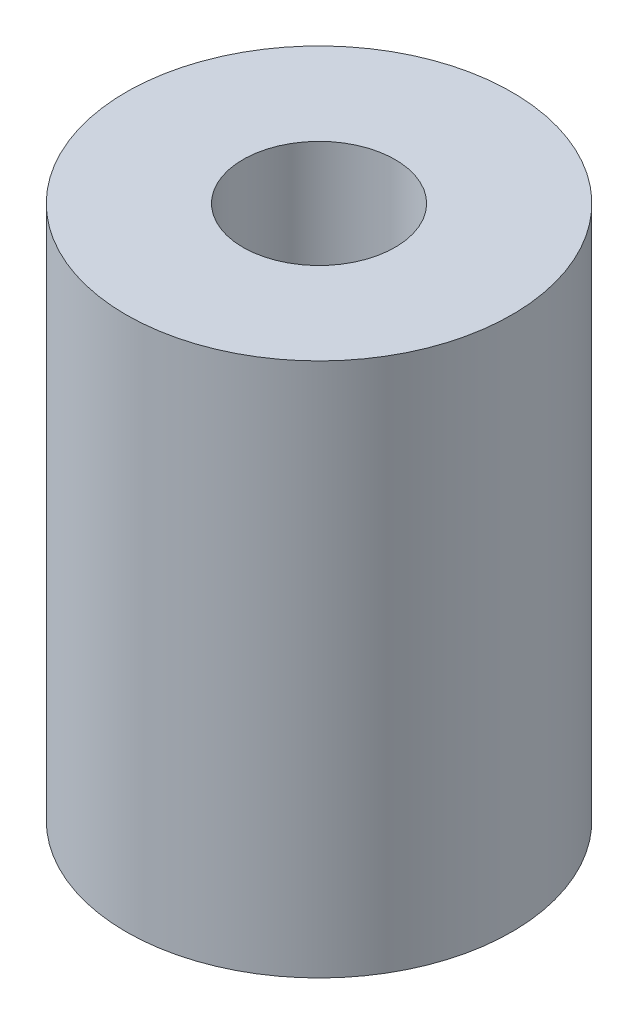
SolidWorks part; units mm, degrees
ref_plane "Front Plane" through (0, 0, 0) normal (0, 0, 1) x (1, 0, 0)
ref_plane "Top Plane" through (0, 0, 0) normal (0, 1, 0) x (1, 0, 0)
ref_plane "Right Plane" through (0, 0, 0) normal (1, 0, 0) x (0, 0, -1)
sketch "Sketch1" plane through (0, 0, 0) normal (0, 1, 0) x (1, 0, 0)
  circle A0 centre (0, 0) radius 8.05
  dimension "D1" = 16.1
extrude "Boss-Extrude1" add sketch "Sketch1" along normal mid plane 22.3
sketch "Sketch2" plane through (0, 11.15, 0) normal (0, 1, 0) x (1, 0, 0)
  circle A0 centre (0, 0) radius 3.175
  dimension "D1" = 6.35
extrude ".25\" hole" cut sketch "Sketch2" against normal blind 7.4
sketch "Sketch3" plane through (0, -11.15, 0) normal (0, -1, 0) x (1, 0, 0)
  circle A0 centre (0, 0) radius 2.54
  dimension "D1" = 5.08
extrude "0.2\" hole" cut sketch "Sketch3" against normal blind 7.4
